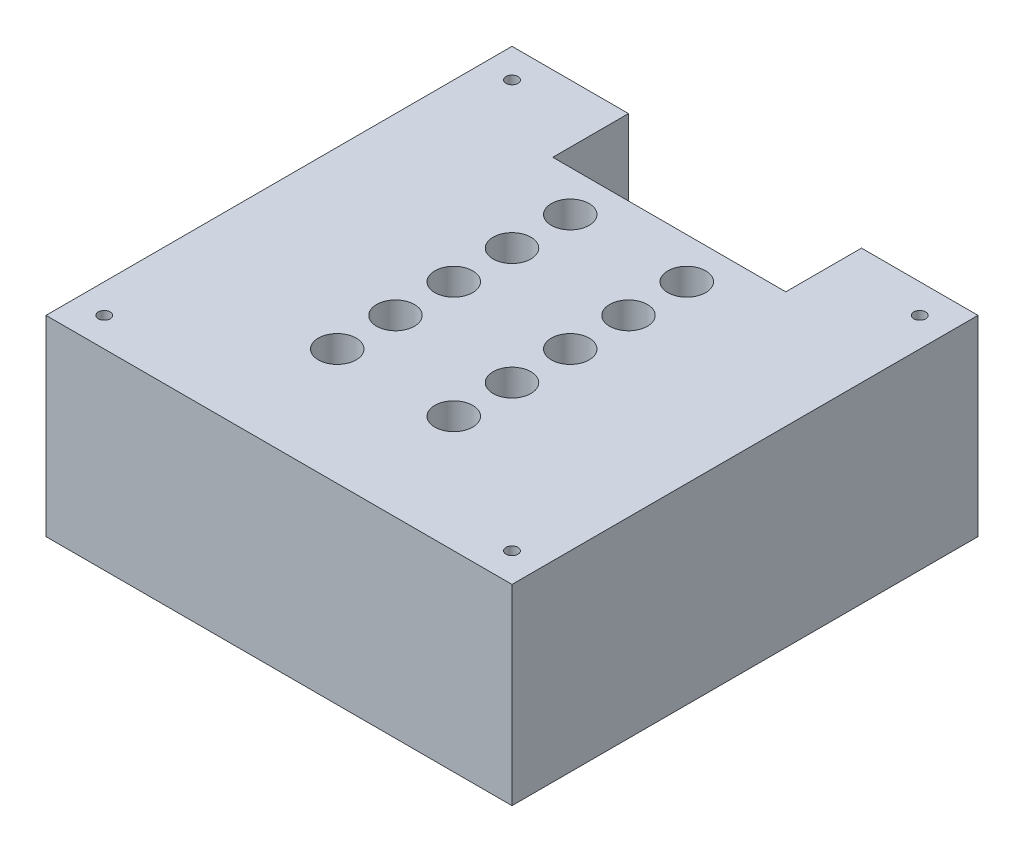
SolidWorks part; units mm, degrees
ref_plane "Front Plane" through (0, 0, 0) normal (0, 0, 1) x (1, 0, 0)
ref_plane "Top Plane" through (0, 0, 0) normal (0, 1, 0) x (1, 0, 0)
ref_plane "Right Plane" through (0, 0, 0) normal (1, 0, 0) x (0, 0, -1)
sketch "Sketch1" plane through (0, 0, 0) normal (0, 1, 0) x (1, 0, 0)
  line L1 (-34.1258, 30.1932) -> (45.8742, 30.1932)
  line L2 (-34.1258, 30.1932) -> (-34.1258, -49.8068)
  line L3 (-34.1258, -49.8068) -> (45.8742, -49.8068)
  line L4 (45.8742, 30.1932) -> (45.8742, -49.8068)
  dimension "D1" = 80
  dimension "D2" = 80
extrude "Boss-Extrude1" add sketch "Sketch1" along normal blind 32.9
sketch "Sketch2" plane through (0, 32.9, 0) normal (0, 1, 0) x (1, 0, 0)
  line L0 (-34.1258, -49.8068) -> (45.8742, -49.8068) construction
  line L1 (-34.1258, 30.1932) -> (-34.1258, -49.8068) construction
  circle A0 centre (-29.1258, -44.8068) radius 1.8619
  circle A1 centre (40.8742, -44.8068) radius 1.8619
  circle A2 centre (40.8742, 25.1932) radius 1.8619
  circle A3 centre (-29.1258, 25.1932) radius 1.8619
  dimension "D3" = 5
  dimension "D4" = 5
  dimension "D1" = 2
  dimension "D2" = 2
hole_wizard "M2.5x0.45 Tapped Hole1" positions "3DSketch1" profile "Sketch3" tap size "M2.5x0.45" standard "ANSI Metric"
sketch3d "3DSketch1"
  point P0 (-29.1258, 32.9, -25.1932)
  point P3 (40.8742, 32.9, -25.1932)
  point P6 (40.8742, 32.9, 44.8068)
  point P9 (-29.1258, 32.9, 44.8068)
cosmetic thread "Hole Thread1" parameters "D2"=2.5
cosmetic thread "Hole Thread2" parameters "D2"=2.5
cosmetic thread "Hole Thread3" parameters "D2"=2.5
cosmetic thread "Hole Thread4" parameters "D2"=2.5
sketch "Sketch3" plane through (-29.1258, 32.9, -25.1932) normal (1, 0, 0) x (0, 0, 1)
  line L0 (0, 0) -> (0, 6.9659)
  line L1 (0, 6.9659) -> (1.025, 6.35)
  line L2 (1.025, 6.35) -> (1.025, 0)
  line L5 (1.025, 0) -> (0, 0)
  line L10 (0, 6.9659) -> (-1.025, 6.35) construction
  line L11 (0, -6.35) -> (0, 107.95) construction
  dimension "Tap Drill Dia." = 2.05
  dimension "Tap Drill Depth" = 6.35
  dimension "Drill Angle" = 118
hole_wizard "CBORE for M3 SHCS1" positions "Sketch21" profile "Sketch23" counterbore size "M3" standard "ANSI Metric" end condition through all
sketch "Sketch21" plane through (0, 32.9, 0) normal (0, 1, 0) x (1, 0, 0)
  line L0 (15.8742, -29.8068) -> (-4.1258, -29.8068) construction
  line L1 (-34.1258, 30.1932) -> (-34.1258, -49.8068) construction
  line L2 (45.8742, 30.1932) -> (-34.1258, 30.1932) construction
  point P0 (15.8742, -29.8068)
  point P7 (-4.1258, -29.8068)
  point P8 (-4.1258, -19.8068)
  point P9 (-4.1258, -9.8068)
  point P10 (-4.1258, 0.1932)
  point P11 (-4.1258, 10.1932)
  point P12 (15.8742, -19.8068)
  point P13 (15.8742, -9.8068)
  point P14 (15.8742, 0.1932)
  point P15 (15.8742, 10.1932)
  dimension "D3" = 20
  dimension "D4" = 30
  dimension "D5" = 30
  dimension "D1" = 2
  dimension "D2" = 5
sketch "Sketch23" plane through (15.8742, 32.9, 29.8068) normal (1, 0, 0) x (0, 0, 1)
  line L0 (0, 0) -> (0, 32.9)
  line L1 (0, 32.9) -> (1.6, 32.9)
  line L3 (1.6, 32.9) -> (1.6, 28)
  line L4 (1.6, 28) -> (3.25, 28)
  line L5 (3.25, 28) -> (3.25, 0)
  line L7 (3.25, 0) -> (0, 0)
  line L11 (0, -6.35) -> (0, 107.95) construction
  dimension "Thru Hole Dia." = 3.2
  dimension "Thru Hole Depth" = 32.9
  dimension "C'Bore Dia." = 6.5
  dimension "C'Bore Depth" = 28
sketch "Sketch25" plane through (0, 0, -30.1932) normal (0, 0, -1) x (-1, 0, 0)
  line L0 (-45.8742, 0) -> (34.1258, 0) construction
  line L1 (-25.8742, 0) -> (14.1258, 0)
  line L2 (-25.8742, 0) -> (-25.8742, 32.9)
  line L3 (-25.8742, 32.9) -> (14.1258, 32.9)
  line L4 (14.1258, 0) -> (14.1258, 32.9)
  line L5 (-45.8742, 32.9) -> (34.1258, 32.9) construction
  line L6 (-45.8742, 32.9) -> (-45.8742, 0) construction
  line L7 (34.1258, 32.9) -> (34.1258, 0) construction
  dimension "D1" = 20
  dimension "D2" = 20
extrude "Cut-Extrude2" cut sketch "Sketch25" against normal blind 13
